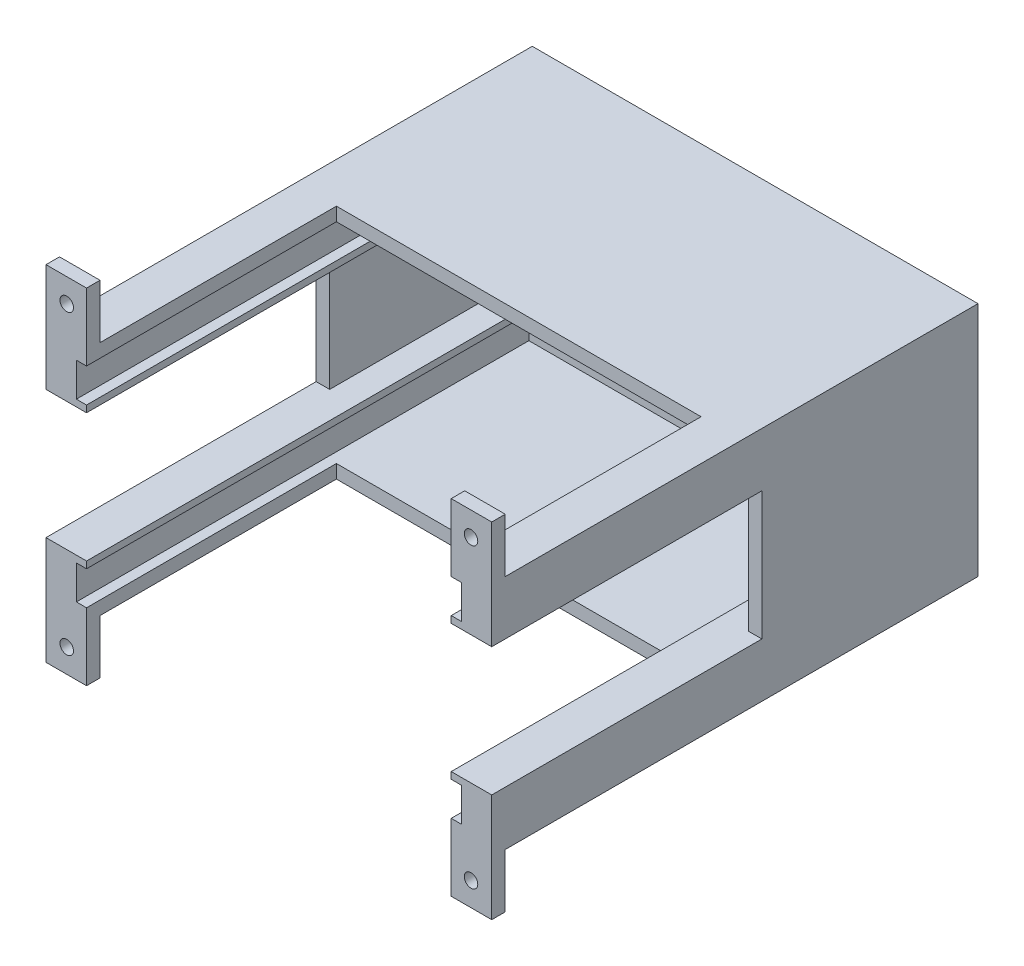
SolidWorks part; units mm, degrees
ref_plane "Plan de face" through (0, 0, 0) normal (0, 0, 1) x (1, 0, 0)
ref_plane "Plan de dessus" through (0, 0, 0) normal (0, 1, 0) x (1, 0, 0)
ref_plane "Plan de droite" through (0, 0, 0) normal (1, 0, 0) x (0, 0, -1)
sketch "Esquisse1" plane through (0, 0, 0) normal (0, 0, 1) x (1, 0, 0)
  line L1 (-33, 17.5) -> (33, 17.5)
  line L2 (-33, 17.5) -> (-33, -17.5)
  line L3 (-33, -17.5) -> (33, -17.5)
  line L4 (33, 17.5) -> (33, -17.5)
  line L5 (-33, 17.5) -> (33, -17.5) construction
  line L6 (-33, -17.5) -> (33, 17.5) construction
  point P0 (0, 0)
  dimension "D1" = 35
  dimension "D2" = 66
extrude "Boss.-Extru.1" add sketch "Esquisse1" along normal blind 70
sketch "Esquisse2" plane through (0, 0, 70) normal (0, 0, 1) x (1, 0, 0)
  line L0 (-33, 17.5) -> (-33, -17.5) construction
  line L1 (-27, 17.5) -> (27, 17.5)
  line L2 (-27, 17.5) -> (-27, -17.5)
  line L3 (-27, -17.5) -> (27, -17.5)
  line L4 (27, 17.5) -> (27, -17.5)
  line L5 (-27, 17.5) -> (27, -17.5) construction
  line L6 (-27, -17.5) -> (27, 17.5) construction
  line L7 (33, -17.5) -> (33, 17.5) construction
  line L8 (33, 17.5) -> (-33, 17.5) construction
  point P0 (0, 0)
  dimension "D1" = 6
  dimension "D2" = 6
  dimension "D3" = 0
extrude "Enlèv. mat.-Extru.2" cut sketch "Esquisse2" against normal blind 65
sketch "Esquisse4" plane through (0, 0, 5) normal (0, 0, 1) x (1, 0, 0)
  line L0 (-27, 17.5) -> (-27, -17.5) construction
  line L1 (-27, 17.5) -> (27, 17.5)
  line L2 (-27, 17.5) -> (-27, 15.5)
  line L3 (-27, 15.5) -> (27, 15.5)
  line L4 (27, 17.5) -> (27, 15.5)
  line L5 (-27, 17.5) -> (-27, -17.5) construction
  line L6 (27, -17.5) -> (27, 17.5) construction
  line L7 (27, 17.5) -> (-27, 17.5) construction
  dimension "D1" = 2
  dimension "D2" = 0
extrude "Boss.-Extru.2" add sketch "Esquisse4" along normal blind 30
mirror "Symétrie1" about plane through (0, 0, 0) normal (0, 1, 0) of "Boss.-Extru.2"
sketch "Esquisse5" plane through (0, 0, 70) normal (0, 0, 1) x (1, 0, 0)
  line L0 (-27, 17.5) -> (-33, 17.5) construction
  line L1 (-33, 25.5) -> (-27, 25.5)
  line L2 (-33, 25.5) -> (-33, -25.5)
  line L3 (-33, -25.5) -> (-27, -25.5)
  line L4 (-27, 25.5) -> (-27, -25.5)
  line L5 (-33, -17.5) -> (-27, -17.5) construction
  dimension "D1" = 6
  dimension "D2" = 8
  dimension "D3" = 8
extrude "Boss.-Extru.3" add sketch "Esquisse5" along normal blind 2
sketch "Esquisse6" plane through (0, 0, 70) normal (0, 0, -1) x (-1, 0, 0)
  line L0 (27, 25.5) -> (33, 25.5) construction
  circle A0 centre (29.9304, 22) radius 1
  dimension "D1" = 2
  dimension "2.5" = 3.5
extrude "Enlèv. mat.-Extru.3" cut sketch "Esquisse6" against normal blind 10
mirror "Symétrie2" about plane through (0, 0, 0) normal (0, 1, 0) of "Enlèv. mat.-Extru.3"
mirror "Symétrie3" about plane through (0, 0, 0) normal (1, 0, 0) of "Symétrie2", "Boss.-Extru.3", "Enlèv. mat.-Extru.3"
sketch "Esquisse12" plane through (0, 0, 0) normal (0, 0, -1) x (-1, 0, 0)
  line L0 (27, -15.5) -> (-27, -15.5) construction
  circle A0 centre (0, -12.5) radius 2.5
  dimension "D1" = 5
  dimension "D2" = 3
extrude "Enlèv. mat.-Extru.5" cut sketch "Esquisse12" against normal blind 0.5
sketch "Esquisse14" plane through (0, 0, 0.5) normal (0, 0, -1) x (-1, 0, 0)
  line L0 (0, -11.25) -> (0, -13.75) construction
  line L5 (0.4, -11.25) -> (0.4, -13.75)
  line L6 (-0.4, -11.25) -> (-0.4, -13.75)
  circle A3 centre (0, -12.5) radius 2.5
  arc A6 (0.4, -11.25) -> (-0.4, -11.25) centre (0, -11.25) ccw
  arc A7 (-0.4, -13.75) -> (0.4, -13.75) centre (0, -13.75) ccw
  point P4 (0, -12.5)
  dimension "D1" = 5
  dimension "D3" = 0.8
  dimension "D2" = 2.5
extrude "Enlèv. mat.-Extru.6" cut sketch "Esquisse14" against normal blind 2 contours L6 A7 L5 A6
sketch "Esquisse15" plane through (0, 0, 0) normal (0, 0, -1) x (-1, 0, 0)
  line L0 (-33, 17.5) -> (33, 17.5) construction
  line L5 (7, -2.5) -> (-5, -2.5)
  line L6 (7, -2.5) -> (7, 9.5)
  line L12 (7, 9.5) -> (-5, 9.5)
  line L17 (-13, -2.5) -> (-25, -2.5)
  line L18 (-13, -2.5) -> (-13, 9.5)
  line L19 (-13, 9.5) -> (-25, 9.5)
  line L20 (-25, -2.5) -> (-25, 9.5)
  line L21 (-13, -2.5) -> (-25, 9.5) construction
  line L22 (-13, 9.5) -> (-25, -2.5) construction
  line L30 (-5, -2.5) -> (-5, 9.5)
  line L31 (7, -2.5) -> (-5, 9.5) construction
  line L32 (7, 9.5) -> (-5, -2.5) construction
  line L33 (25, -3.5) -> (15, -3.5)
  line L34 (25, -3.5) -> (25, 11.5)
  line L35 (25, 11.5) -> (15, 11.5)
  line L36 (15, -3.5) -> (15, 11.5)
  line L37 (25, -3.5) -> (15, 11.5) construction
  line L38 (25, 11.5) -> (15, -3.5) construction
  line L39 (33, 17.5) -> (33, -17.5) construction
  line L40 (-33, -17.5) -> (-33, 17.5) construction
  point P2 (1, 3.5)
  point P7 (20, 4)
  point P11 (-19, 3.5)
  dimension "D1" = 8
  dimension "D2" = 12
  dimension "D3" = 12
  dimension "D4" = 8
  dimension "D5" = 12
  dimension "D6" = 12
  dimension "D7" = 8
  dimension "D8" = 15
  dimension "D9" = 10
  dimension "D10" = 6
  dimension "D11" = 8
  dimension "D12" = 8
extrude "Enlèv. mat.-Extru.8" cut sketch "Esquisse15" against normal blind 3
sketch "Esquisse17" plane through (-33, 0, 0) normal (-1, 0, 0) x (0, 0, 1)
  line L0 (0, 17.5) -> (0, -17.5) construction
  line L1 (32, 9.5) -> (72, 9.5)
  line L2 (32, 9.5) -> (32, -9.5)
  line L3 (32, -9.5) -> (72, -9.5)
  line L4 (72, 9.5) -> (72, -9.5)
  line L5 (32, 9.5) -> (72, -9.5) construction
  line L6 (32, -9.5) -> (72, 9.5) construction
  line L7 (70, 17.5) -> (0, 17.5) construction
  line L8 (70, -17.5) -> (0, -17.5) construction
  line L9 (72, 25.5) -> (72, -25.5) construction
  point P0 (52, 0)
  dimension "D1" = 32
  dimension "D2" = 8
  dimension "D3" = 8
  dimension "D4" = 0
extrude "Enlèv. mat.-Extru.10" cut sketch "Esquisse17" against normal through all
sketch "Esquisse18" plane through (0, 0, 32) normal (0, 0, 1) x (1, 0, 0)
  line L0 (27, -9.5) -> (27, 9.5) construction
  line L1 (27, 9.5) -> (31, 9.5)
  line L2 (27, 9.5) -> (27, -9.5)
  line L3 (27, -9.5) -> (31, -9.5)
  line L4 (31, 9.5) -> (31, -9.5)
  line L5 (33, 9.5) -> (33, -9.5) construction
  line L8 (33, -9.5) -> (27, -9.5) construction
  line L9 (33, 9.5) -> (27, 9.5) construction
  dimension "D1" = 2
  dimension "D2" = 0
  dimension "D3" = 0
extrude "Enlèv. mat.-Extru.11" cut sketch "Esquisse18" against normal blind 30
sketch "Esquisse20" plane through (27, 0, 0) normal (-1, 0, 0) x (0, 0, 1)
  line L0 (72, -25.5) -> (72, -9.5) construction
  line L1 (5, -10.5) -> (72, -10.5)
  line L2 (5, -10.5) -> (5, -15.5)
  line L3 (5, -15.5) -> (72, -15.5)
  line L4 (72, -10.5) -> (72, -15.5)
  line L5 (72, -9.5) -> (5, -9.5) construction
  line L6 (35, -17.5) -> (70, -17.5) construction
  line L7 (5, -15.5) -> (5, -9.5) construction
  dimension "D1" = 1
  dimension "D2" = 2
  dimension "D3" = 5
  dimension "D4" = 0
extrude "Enlèv. mat.-Extru.13" cut sketch "Esquisse20" against normal blind 1.5
mirror "Symétrie4" about plane through (0, 0, 0) normal (0, 1, 0) of "Enlèv. mat.-Extru.13"
mirror "Symétrie5" about plane through (0, 0, 0) normal (1, 0, 0) of "Symétrie4", "Enlèv. mat.-Extru.13", "Enlèv. mat.-Extru.11"
sketch "Esquisse22" plane through (0, 0, 0) normal (0, 0, -1) x (-1, 0, 0)
  line L0 (-13, -2.5) -> (-13, 9.5) construction
  line L1 (-13, 7) -> (-12, 7)
  line L2 (-13, 7) -> (-13, 0)
  line L3 (-13, 0) -> (-12, 0)
  line L4 (-12, 7) -> (-12, 0)
  line L5 (-25, 9.5) -> (-25, -2.5) construction
  line L6 (-25, 7) -> (-26, 7)
  line L7 (-25, 7) -> (-25, 0)
  line L8 (-25, 0) -> (-26, 0)
  line L9 (-26, 7) -> (-26, 0)
  line L10 (-5, 9.5) -> (-5, -2.5) construction
  line L11 (-5, 7) -> (-6, 7)
  line L12 (-5, 7) -> (-5, 0)
  line L13 (-5, 0) -> (-6, 0)
  line L14 (-6, 7) -> (-6, 0)
  line L15 (7, -2.5) -> (7, 9.5) construction
  line L16 (7, 7) -> (8, 7)
  line L17 (7, 7) -> (7, 0)
  line L18 (7, 0) -> (8, 0)
  line L19 (8, 7) -> (8, 0)
  line L20 (-5, -2.5) -> (7, -2.5) construction
  dimension "D1" = 7
  dimension "D2" = 7
  dimension "D3" = 2.5
  dimension "D4" = 2.5
  dimension "D5" = 1
  dimension "D6" = 1
  dimension "D7" = 7
  dimension "D8" = 2.5
  dimension "D9" = 7
  dimension "D10" = 2.5
  dimension "D11" = 1
  dimension "D12" = 1
extrude "Enlèv. mat.-Extru.14" cut sketch "Esquisse22" against normal through all
